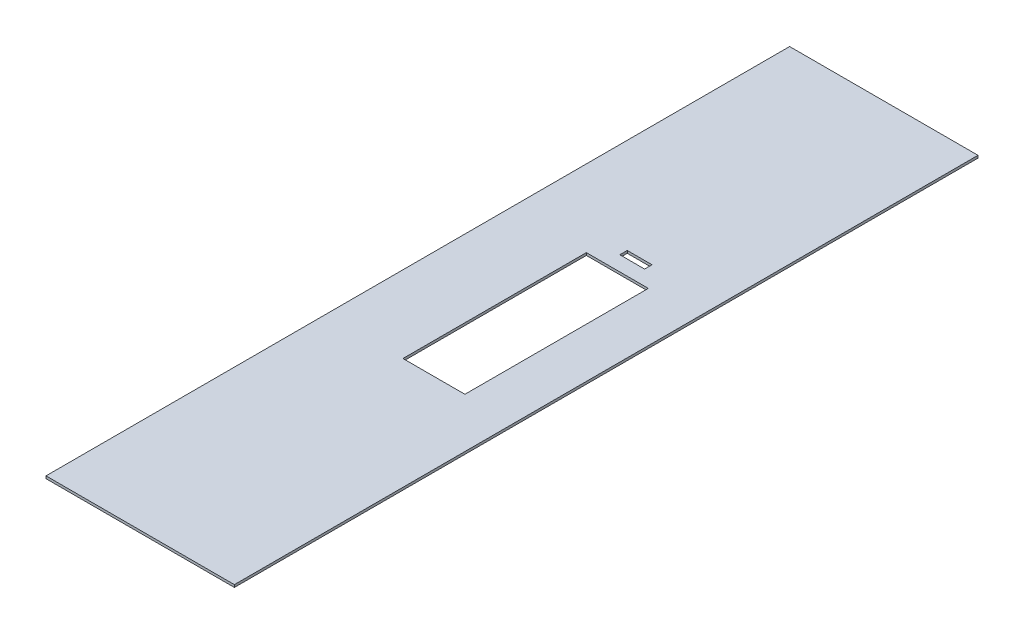
SolidWorks part; units mm, degrees
ref_plane "Ebene vorne" through (0, 0, 0) normal (0, 0, 1) x (1, 0, 0)
ref_plane "Ebene oben" through (0, 0, 0) normal (0, 1, 0) x (1, 0, 0)
ref_plane "Ebene rechts" through (0, 0, 0) normal (1, 0, 0) x (0, 0, -1)
sketch "Skizze1" plane through (0, 0, 0) normal (0, 0, 1) x (1, 0, 0)
  line L0 (0, 0) -> (76, 0)
  dimension "D1" = 76
extrude "Linear-Austragen-Dünn1" add sketch "Skizze1" along normal blind 300 thin
sketch "Skizze2" plane through (0, -1, 0) normal (0, -1, 0) x (1, 0, 0)
  line L0 (56, 113) -> (56, 0) construction
  line L1 (56, 187) -> (31, 187)
  line L2 (56, 187) -> (56, 113)
  line L3 (56, 113) -> (31, 113)
  line L4 (31, 187) -> (31, 113)
  line L5 (0, 0) -> (76, 0) construction
  line L6 (56, 187) -> (56, 300) construction
  line L7 (0, 300) -> (76, 300) construction
  line L8 (56, 187) -> (76, 187) construction
  line L9 (76, 300) -> (76, 0) construction
  line L10 (31, 187) -> (0, 187) construction
  line L11 (0, 300) -> (0, 0) construction
  line L12 (48.5, 107) -> (56, 113) construction
  line L13 (48.5, 107) -> (38.5, 107)
  line L14 (48.5, 107) -> (48.5, 104)
  line L15 (48.5, 104) -> (38.5, 104)
  line L16 (38.5, 107) -> (38.5, 104)
  line L17 (38.5, 107) -> (31, 113) construction
  dimension "D1" = 25
  dimension "D2" = 20
  dimension "D3" = 74
  dimension "D4" = 3
  dimension "D5" = 10
  dimension "D6" = 6
extrude "Schnitt-Linear austragen1" cut sketch "Skizze2" against normal blind 10
